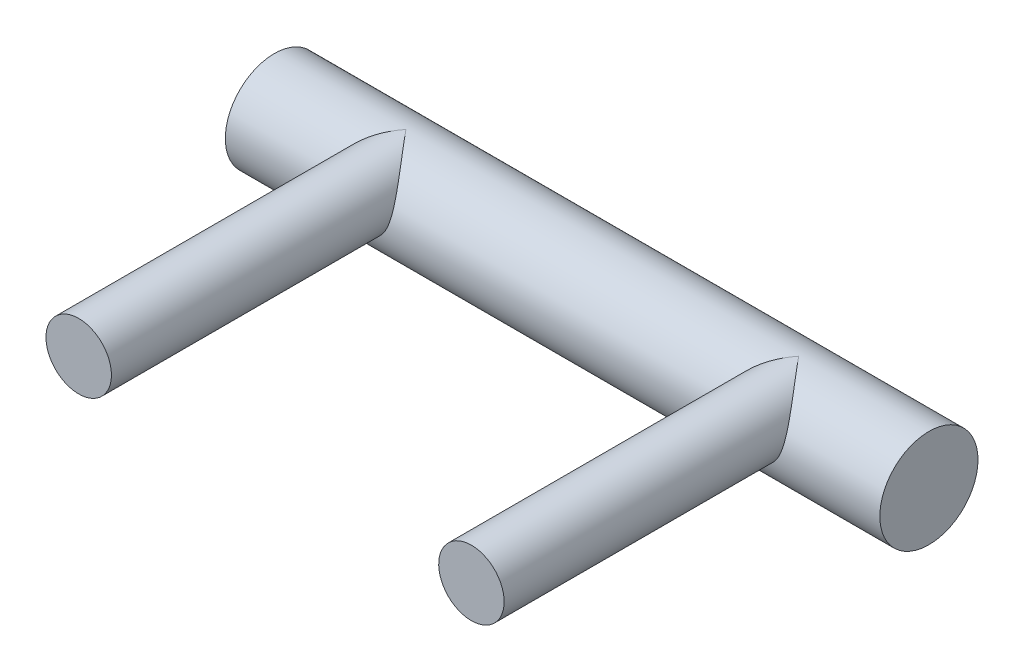
SolidWorks part; units mm, degrees
material "AISI 1015 Steel, Cold Drawn (SS)"
ref_plane "Front Plane" through (0, 0, 0) normal (0, 0, 1) x (1, 0, 0)
ref_plane "Top Plane" through (0, 0, 0) normal (0, 1, 0) x (1, 0, 0)
ref_plane "Right Plane" through (0, 0, 0) normal (1, 0, 0) x (0, 0, -1)
sketch "Sketch3" plane through (0, 0, 0) normal (1, 0, 0) x (0, 0, -1)
  circle A0 centre (0, 0) radius 9.525
  dimension "D1" = 19.05
extrude "Boss-Extrude1" add sketch "Sketch3" along normal mid plane 127
sketch "Sketch4" plane through (0, 0, 0) normal (0, 0, 1) x (1, 0, 0)
  line L1 (-63.5, -9.525) -> (63.5, -9.525) construction
  circle A0 centre (-37.9675, 3.175) radius 6.35
  circle A1 centre (38.2325, 3.175) radius 6.35
  point P4 (0, 0)
  dimension "D1" = 76.2
  dimension "D2" = 12.7
  dimension "D3" = 12.7
  dimension "D4" = 12.7
  dimension "D5" = 38.1
  dimension "D6" = 12.7
extrude "Boss-Extrude2" add sketch "Sketch4" along normal blind 63.5
